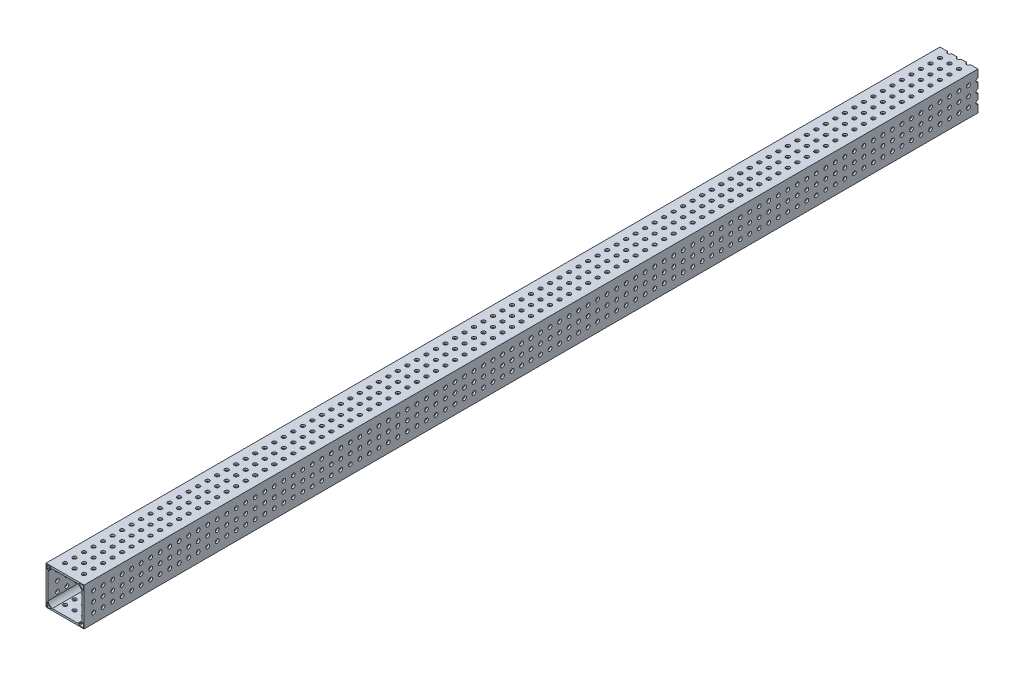
SolidWorks part; units mm, degrees
material "6061 Alloy"
ref_plane "Front Plane" through (0, 0, 0) normal (0, 0, 1) x (1, 0, 0)
ref_plane "Top Plane" through (0, 0, 0) normal (0, 1, 0) x (1, 0, 0)
ref_plane "Right Plane" through (0, 0, 0) normal (1, 0, 0) x (0, 0, -1)
other "Configuration Table"
sketch "Sketch1" plane through (0, 0, 0) normal (0, 0, 1) x (1, 0, 0)
  line L1 (-25.4, -25.4) -> (25.4, -25.4)
  line L2 (-25.4, -25.4) -> (-25.4, 25.4)
  line L3 (-25.4, 25.4) -> (25.4, 25.4)
  line L4 (25.4, -25.4) -> (25.4, 25.4)
  line L5 (-25.4, -25.4) -> (25.4, 25.4) construction
  line L6 (-25.4, 25.4) -> (25.4, -25.4) construction
  point P0 (0, 0)
  dimension "D1" = 50.8
extrude "Boss-Extrude1" add sketch "Sketch1" along normal mid plane 1193.8
sketch "Sketch2" plane through (0, 0, 596.9) normal (0, 0, 1) x (1, 0, 0)
  line L10 (0, 0) -> (0, 22.9141)
  line L11 (-22.9141, 0) -> (0, 0)
  line L12 (-22.9141, 17.0772) -> (-22.9141, 0)
  line L13 (0, 22.9141) -> (-17.0772, 22.9141)
  line L14 (-24.384, 23.6924) -> (-24.384, 19.2971)
  line L15 (-19.2971, 24.384) -> (-23.6924, 24.384)
  line L16 (25.4, -25.4) -> (25.4, 25.4) construction
  arc A12 (-17.0772, 22.9141) -> (-22.9141, 17.0772) centre (-12.7, 12.7) ccw
  arc A13 (-18.9412, 23.0994) -> (-23.0994, 18.9412) centre (-12.7, 12.7) ccw
  arc A14 (-24.384, 19.2971) -> (-23.0994, 18.9412) centre (-23.6924, 19.2971) ccw
  arc A15 (-23.6924, 24.384) -> (-24.384, 23.6924) centre (-23.6924, 23.6924) ccw
  arc A16 (-18.6055, 23.6924) -> (-19.2971, 24.384) centre (-19.2971, 23.6924) ccw
  arc A17 (-18.9412, 23.0994) -> (-18.6055, 23.6924) centre (-19.2971, 23.6924) ccw
  dimension "D1" = 11.1125
  dimension "D2" = 12.1285
  dimension "D3" = 0.6916
  dimension "D4" = 12.7
  dimension "D5" = 42.4772
  dimension "D6" = 44.0055
extrude "Cut-Extrude1" cut sketch "Sketch2" against normal through all
mirror "Mirror1" about plane through (0, 0, 0) normal (1, 0, 0) of "Cut-Extrude1" second plane through (0, 0, 0) second plane normal (0, 1, 0)
sketch "Sketch4" plane through (0, 25.4, 0) normal (0, 1, 0) x (1, 0, 0)
  line L0 (25.4, -596.9) -> (-25.4, -596.9) construction
  line L1 (-25.4, -596.9) -> (-25.4, 596.9) construction
  circle A0 centre (-12.7, -584.2) radius 2.54
  circle A1 centre (-12.7, -571.5) radius 2.54
  circle A2 centre (-12.7, -558.8) radius 2.54
  circle A3 centre (-12.7, -546.1) radius 2.54
  circle A4 centre (-12.7, -533.4) radius 2.54
  circle A5 centre (-12.7, -520.7) radius 2.54
  circle A6 centre (-12.7, -508) radius 2.54
  circle A7 centre (-12.7, -495.3) radius 2.54
  circle A8 centre (-12.7, -482.6) radius 2.54
  circle A9 centre (-12.7, -469.9) radius 2.54
  circle A10 centre (-12.7, -457.2) radius 2.54
  circle A11 centre (-12.7, -444.5) radius 2.54
  circle A12 centre (-12.7, -431.8) radius 2.54
  circle A13 centre (-12.7, -419.1) radius 2.54
  circle A14 centre (-12.7, -406.4) radius 2.54
  circle A15 centre (-12.7, -393.7) radius 2.54
  circle A16 centre (-12.7, -381) radius 2.54
  circle A17 centre (-12.7, -368.3) radius 2.54
  circle A18 centre (-12.7, -355.6) radius 2.54
  circle A19 centre (-12.7, -342.9) radius 2.54
  circle A20 centre (-12.7, -330.2) radius 2.54
  circle A21 centre (-12.7, -317.5) radius 2.54
  circle A22 centre (-12.7, -304.8) radius 2.54
  circle A23 centre (-12.7, -292.1) radius 2.54
  circle A24 centre (-12.7, -279.4) radius 2.54
  circle A25 centre (-12.7, -266.7) radius 2.54
  circle A26 centre (-12.7, -254) radius 2.54
  circle A27 centre (-12.7, -241.3) radius 2.54
  circle A28 centre (-12.7, -228.6) radius 2.54
  circle A29 centre (-12.7, -215.9) radius 2.54
  circle A30 centre (-12.7, -203.2) radius 2.54
  circle A31 centre (-12.7, -190.5) radius 2.54
  circle A32 centre (-12.7, -177.8) radius 2.54
  circle A33 centre (-12.7, -165.1) radius 2.54
  circle A34 centre (-12.7, -152.4) radius 2.54
  circle A35 centre (-12.7, -139.7) radius 2.54
  circle A36 centre (-12.7, -127) radius 2.54
  circle A37 centre (-12.7, -114.3) radius 2.54
  circle A38 centre (-12.7, -101.6) radius 2.54
  circle A39 centre (-12.7, -88.9) radius 2.54
  circle A40 centre (-12.7, -76.2) radius 2.54
  circle A41 centre (-12.7, -63.5) radius 2.54
  circle A42 centre (-12.7, -50.8) radius 2.54
  circle A43 centre (-12.7, -38.1) radius 2.54
  circle A44 centre (-12.7, -25.4) radius 2.54
  circle A45 centre (-12.7, -12.7) radius 2.54
  circle A46 centre (-12.7, 0) radius 2.54
  circle A47 centre (-12.7, 12.7) radius 2.54
  circle A48 centre (-12.7, 25.4) radius 2.54
  circle A49 centre (-12.7, 38.1) radius 2.54
  circle A50 centre (-12.7, 50.8) radius 2.54
  circle A51 centre (-12.7, 63.5) radius 2.54
  circle A52 centre (-12.7, 76.2) radius 2.54
  circle A53 centre (-12.7, 88.9) radius 2.54
  circle A54 centre (-12.7, 101.6) radius 2.54
  circle A55 centre (-12.7, 114.3) radius 2.54
  circle A56 centre (-12.7, 127) radius 2.54
  circle A57 centre (-12.7, 139.7) radius 2.54
  circle A58 centre (-12.7, 152.4) radius 2.54
  circle A59 centre (-12.7, 165.1) radius 2.54
  circle A60 centre (-12.7, 177.8) radius 2.54
  circle A61 centre (-12.7, 190.5) radius 2.54
  circle A62 centre (-12.7, 203.2) radius 2.54
  circle A63 centre (-12.7, 215.9) radius 2.54
  circle A64 centre (-12.7, 228.6) radius 2.54
  circle A65 centre (-12.7, 241.3) radius 2.54
  circle A66 centre (-12.7, 254) radius 2.54
  circle A67 centre (-12.7, 266.7) radius 2.54
  circle A68 centre (-12.7, 279.4) radius 2.54
  circle A69 centre (-12.7, 292.1) radius 2.54
  circle A70 centre (-12.7, 304.8) radius 2.54
  circle A71 centre (-12.7, 317.5) radius 2.54
  circle A72 centre (-12.7, 330.2) radius 2.54
  circle A73 centre (-12.7, 342.9) radius 2.54
  circle A74 centre (-12.7, 355.6) radius 2.54
  circle A75 centre (-12.7, 368.3) radius 2.54
  circle A76 centre (-12.7, 381) radius 2.54
  circle A77 centre (-12.7, 393.7) radius 2.54
  circle A78 centre (-12.7, 406.4) radius 2.54
  circle A79 centre (-12.7, 419.1) radius 2.54
  circle A80 centre (-12.7, 431.8) radius 2.54
  circle A81 centre (-12.7, 444.5) radius 2.54
  circle A82 centre (-12.7, 457.2) radius 2.54
  circle A83 centre (-12.7, 469.9) radius 2.54
  circle A84 centre (-12.7, 482.6) radius 2.54
  circle A85 centre (-12.7, 495.3) radius 2.54
  circle A86 centre (-12.7, 508) radius 2.54
  circle A87 centre (-12.7, 520.7) radius 2.54
  circle A88 centre (-12.7, 533.4) radius 2.54
  circle A89 centre (-12.7, 546.1) radius 2.54
  circle A90 centre (-12.7, 558.8) radius 2.54
  circle A91 centre (-12.7, 571.5) radius 2.54
  circle A92 centre (-12.7, 584.2) radius 2.54
  circle A93 centre (-12.7, 596.9) radius 2.54
  circle A94 centre (0, -571.5) radius 2.54
  circle A95 centre (0, -558.8) radius 2.54
  circle A96 centre (0, -546.1) radius 2.54
  circle A97 centre (0, -533.4) radius 2.54
  circle A98 centre (0, -520.7) radius 2.54
  circle A99 centre (0, -508) radius 2.54
  circle A100 centre (0, -495.3) radius 2.54
  circle A101 centre (0, -482.6) radius 2.54
  circle A102 centre (0, -469.9) radius 2.54
  circle A103 centre (0, -457.2) radius 2.54
  circle A104 centre (0, -444.5) radius 2.54
  circle A105 centre (0, -431.8) radius 2.54
  circle A106 centre (0, -419.1) radius 2.54
  circle A107 centre (0, -406.4) radius 2.54
  circle A108 centre (0, -393.7) radius 2.54
  circle A109 centre (0, -381) radius 2.54
  circle A110 centre (0, -368.3) radius 2.54
  circle A111 centre (0, -355.6) radius 2.54
  circle A112 centre (0, -342.9) radius 2.54
  circle A113 centre (0, -330.2) radius 2.54
  circle A114 centre (0, -317.5) radius 2.54
  circle A115 centre (0, -304.8) radius 2.54
  circle A116 centre (0, -292.1) radius 2.54
  circle A117 centre (0, -279.4) radius 2.54
  circle A118 centre (0, -266.7) radius 2.54
  circle A119 centre (0, -254) radius 2.54
  circle A120 centre (0, -241.3) radius 2.54
  circle A121 centre (0, -228.6) radius 2.54
  circle A122 centre (0, -215.9) radius 2.54
  circle A123 centre (0, -203.2) radius 2.54
  circle A124 centre (0, -190.5) radius 2.54
  circle A125 centre (0, -177.8) radius 2.54
  circle A126 centre (0, -165.1) radius 2.54
  circle A127 centre (0, -152.4) radius 2.54
  circle A128 centre (0, -139.7) radius 2.54
  circle A129 centre (0, -127) radius 2.54
  circle A130 centre (0, -114.3) radius 2.54
  circle A131 centre (0, -101.6) radius 2.54
  circle A132 centre (0, -88.9) radius 2.54
  circle A133 centre (0, -76.2) radius 2.54
  circle A134 centre (0, -63.5) radius 2.54
  circle A135 centre (0, -50.8) radius 2.54
  circle A136 centre (0, -38.1) radius 2.54
  circle A137 centre (0, -25.4) radius 2.54
  circle A138 centre (0, -12.7) radius 2.54
  circle A139 centre (0, 0) radius 2.54
  circle A140 centre (0, 12.7) radius 2.54
  circle A141 centre (0, 25.4) radius 2.54
  circle A142 centre (0, 38.1) radius 2.54
  circle A143 centre (0, 50.8) radius 2.54
  circle A144 centre (0, 63.5) radius 2.54
  circle A145 centre (0, 76.2) radius 2.54
  circle A146 centre (0, 88.9) radius 2.54
  circle A147 centre (0, 101.6) radius 2.54
  circle A148 centre (0, 114.3) radius 2.54
  circle A149 centre (0, 127) radius 2.54
  circle A150 centre (0, 139.7) radius 2.54
  circle A151 centre (0, 152.4) radius 2.54
  circle A152 centre (0, 165.1) radius 2.54
  circle A153 centre (0, 177.8) radius 2.54
  circle A154 centre (0, 190.5) radius 2.54
  circle A155 centre (0, 203.2) radius 2.54
  circle A156 centre (0, 215.9) radius 2.54
  circle A157 centre (0, 228.6) radius 2.54
  circle A158 centre (0, 241.3) radius 2.54
  circle A159 centre (0, 254) radius 2.54
  circle A160 centre (0, 266.7) radius 2.54
  circle A161 centre (0, 279.4) radius 2.54
  circle A162 centre (0, 292.1) radius 2.54
  circle A163 centre (0, 304.8) radius 2.54
  circle A164 centre (0, 317.5) radius 2.54
  circle A165 centre (0, 330.2) radius 2.54
  circle A166 centre (0, 342.9) radius 2.54
  circle A167 centre (0, 355.6) radius 2.54
  circle A168 centre (0, 368.3) radius 2.54
  circle A169 centre (0, 381) radius 2.54
  circle A170 centre (0, 393.7) radius 2.54
  circle A171 centre (0, 406.4) radius 2.54
  circle A172 centre (0, 419.1) radius 2.54
  circle A173 centre (0, 431.8) radius 2.54
  circle A174 centre (0, 444.5) radius 2.54
  circle A175 centre (0, 457.2) radius 2.54
  circle A176 centre (0, 469.9) radius 2.54
  circle A177 centre (0, 482.6) radius 2.54
  circle A178 centre (0, 495.3) radius 2.54
  circle A179 centre (0, 508) radius 2.54
  circle A180 centre (0, 520.7) radius 2.54
  circle A181 centre (0, 533.4) radius 2.54
  circle A182 centre (0, 546.1) radius 2.54
  circle A183 centre (0, 558.8) radius 2.54
  circle A184 centre (0, 571.5) radius 2.54
  circle A185 centre (0, 584.2) radius 2.54
  circle A186 centre (0, 596.9) radius 2.54
  circle A187 centre (12.7, -571.5) radius 2.54
  circle A188 centre (12.7, -558.8) radius 2.54
  circle A189 centre (12.7, -546.1) radius 2.54
  circle A190 centre (12.7, -533.4) radius 2.54
  circle A191 centre (12.7, -520.7) radius 2.54
  circle A192 centre (12.7, -508) radius 2.54
  circle A193 centre (12.7, -495.3) radius 2.54
  circle A194 centre (12.7, -482.6) radius 2.54
  circle A195 centre (12.7, -469.9) radius 2.54
  circle A196 centre (12.7, -457.2) radius 2.54
  circle A197 centre (12.7, -444.5) radius 2.54
  circle A198 centre (12.7, -431.8) radius 2.54
  circle A199 centre (12.7, -419.1) radius 2.54
  circle A200 centre (12.7, -406.4) radius 2.54
  circle A201 centre (12.7, -393.7) radius 2.54
  circle A202 centre (12.7, -381) radius 2.54
  circle A203 centre (12.7, -368.3) radius 2.54
  circle A204 centre (12.7, -355.6) radius 2.54
  circle A205 centre (12.7, -342.9) radius 2.54
  circle A206 centre (12.7, -330.2) radius 2.54
  circle A207 centre (12.7, -317.5) radius 2.54
  circle A208 centre (12.7, -304.8) radius 2.54
  circle A209 centre (12.7, -292.1) radius 2.54
  circle A210 centre (12.7, -279.4) radius 2.54
  circle A211 centre (12.7, -266.7) radius 2.54
  circle A212 centre (12.7, -254) radius 2.54
  circle A213 centre (12.7, -241.3) radius 2.54
  circle A214 centre (12.7, -228.6) radius 2.54
  circle A215 centre (12.7, -215.9) radius 2.54
  circle A216 centre (12.7, -203.2) radius 2.54
  circle A217 centre (12.7, -190.5) radius 2.54
  circle A218 centre (12.7, -177.8) radius 2.54
  circle A219 centre (12.7, -165.1) radius 2.54
  circle A220 centre (12.7, -152.4) radius 2.54
  circle A221 centre (12.7, -139.7) radius 2.54
  circle A222 centre (12.7, -127) radius 2.54
  circle A223 centre (12.7, -114.3) radius 2.54
  circle A224 centre (12.7, -101.6) radius 2.54
  circle A225 centre (12.7, -88.9) radius 2.54
  circle A226 centre (12.7, -76.2) radius 2.54
  circle A227 centre (12.7, -63.5) radius 2.54
  circle A228 centre (12.7, -50.8) radius 2.54
  circle A229 centre (12.7, -38.1) radius 2.54
  circle A230 centre (12.7, -25.4) radius 2.54
  circle A231 centre (12.7, -12.7) radius 2.54
  circle A232 centre (12.7, 0) radius 2.54
  circle A233 centre (12.7, 12.7) radius 2.54
  circle A234 centre (12.7, 25.4) radius 2.54
  circle A235 centre (12.7, 38.1) radius 2.54
  circle A236 centre (12.7, 50.8) radius 2.54
  circle A237 centre (12.7, 63.5) radius 2.54
  circle A238 centre (12.7, 76.2) radius 2.54
  circle A239 centre (12.7, 88.9) radius 2.54
  circle A240 centre (12.7, 101.6) radius 2.54
  circle A241 centre (12.7, 114.3) radius 2.54
  circle A242 centre (12.7, 127) radius 2.54
  circle A243 centre (12.7, 139.7) radius 2.54
  circle A244 centre (12.7, 152.4) radius 2.54
  circle A245 centre (12.7, 165.1) radius 2.54
  circle A246 centre (12.7, 177.8) radius 2.54
  circle A247 centre (12.7, 190.5) radius 2.54
  circle A248 centre (12.7, 203.2) radius 2.54
  circle A249 centre (12.7, 215.9) radius 2.54
  circle A250 centre (12.7, 228.6) radius 2.54
  circle A251 centre (12.7, 241.3) radius 2.54
  circle A252 centre (12.7, 254) radius 2.54
  circle A253 centre (12.7, 266.7) radius 2.54
  circle A254 centre (12.7, 279.4) radius 2.54
  circle A255 centre (12.7, 292.1) radius 2.54
  circle A256 centre (12.7, 304.8) radius 2.54
  circle A257 centre (12.7, 317.5) radius 2.54
  circle A258 centre (12.7, 330.2) radius 2.54
  circle A259 centre (12.7, 342.9) radius 2.54
  circle A260 centre (12.7, 355.6) radius 2.54
  circle A261 centre (12.7, 368.3) radius 2.54
  circle A262 centre (12.7, 381) radius 2.54
  circle A263 centre (12.7, 393.7) radius 2.54
  circle A264 centre (12.7, 406.4) radius 2.54
  circle A265 centre (12.7, 419.1) radius 2.54
  circle A266 centre (12.7, 431.8) radius 2.54
  circle A267 centre (12.7, 444.5) radius 2.54
  circle A268 centre (12.7, 457.2) radius 2.54
  circle A269 centre (12.7, 469.9) radius 2.54
  circle A270 centre (12.7, 482.6) radius 2.54
  circle A271 centre (12.7, 495.3) radius 2.54
  circle A272 centre (12.7, 508) radius 2.54
  circle A273 centre (12.7, 520.7) radius 2.54
  circle A274 centre (12.7, 533.4) radius 2.54
  circle A275 centre (12.7, 546.1) radius 2.54
  circle A276 centre (12.7, 558.8) radius 2.54
  circle A277 centre (12.7, 571.5) radius 2.54
  circle A278 centre (12.7, 584.2) radius 2.54
  circle A279 centre (12.7, 596.9) radius 2.54
  circle A280 centre (0, -584.2) radius 2.54
  circle A281 centre (12.7, -584.2) radius 2.54
  point P6 (0, 0)
  point P7 (0, 0)
  dimension "D1" = 2.54
  dimension "D2" = 12.7
  dimension "D3" = 12.7
  dimension "D6" = 1181.1
  dimension "D7" = 12.7
  dimension "D4" = 94
  dimension "D5" = 3
extrude "Cut-Extrude2" cut sketch "Sketch4" against normal through all
ref_plane "Plane1" through (0, 0, 0) normal (-0.7071, 0.7071, 0) x (0.7071, 0.7071, 0)
mirror "Mirror2" about plane through (0, 0, 0) normal (-0.7071, 0.7071, 0) of "Cut-Extrude2"
equation "\"Length\" = 47"
equation "\"D1@Boss-Extrude1\"= \"Length\""
